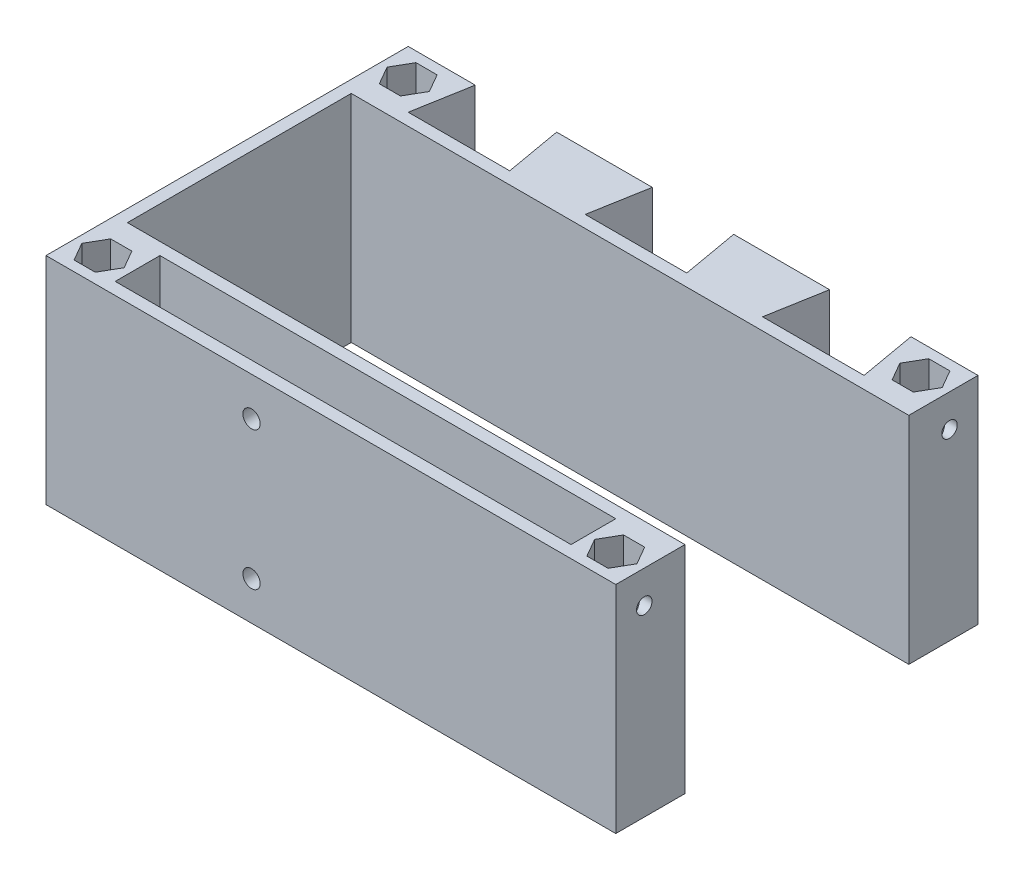
SolidWorks part; units mm, degrees
ref_plane "Front Plane" through (0, 0, 0) normal (0, 0, 1) x (1, 0, 0)
ref_plane "Top Plane" through (0, 0, 0) normal (0, 1, 0) x (1, 0, 0)
ref_plane "Right Plane" through (0, 0, 0) normal (1, 0, 0) x (0, 0, -1)
sketch "Sketch1" plane through (0, 0, 0) normal (0, 1, 0) x (1, 0, 0)
  line L0 (0, 0) -> (140, 0)
  line L1 (140, 0) -> (140, 55)
  line L2 (140, 55) -> (0, 55)
  line L3 (0, 55) -> (0, 0)
  line L4 (140, 58) -> (0, 58)
  line L5 (0, -3) -> (140, -3)
  line L6 (0, 55) -> (0, 58)
  line L7 (0, -3) -> (0, 0)
  line L8 (140, -3) -> (140, 0)
  line L9 (140, 55) -> (140, 58)
  line L10 (0, 27.5) -> (140, 27.5) construction
  line L11 (0, 58) -> (0, 72)
  line L12 (0, 72) -> (14, 72)
  line L13 (14, 72) -> (14, 58)
  line L14 (14, 58) -> (0, 58)
  line L15 (7, 72) -> (7, 58) construction
  line L16 (4.4019, -5.5) -> (9.5981, -5.5)
  line L17 (1.8038, 65) -> (12.1962, 65) construction
  line L18 (12.1962, 65) -> (9.5981, 69.5)
  line L19 (9.5981, 69.5) -> (4.4019, 69.5)
  line L20 (4.4019, 69.5) -> (1.8038, 65)
  line L21 (1.8038, 65) -> (4.4019, 60.5)
  line L22 (4.4019, 60.5) -> (9.5981, 60.5)
  line L23 (9.5981, 60.5) -> (12.1962, 65)
  line L24 (1.8038, -10) -> (12.1962, -10) construction
  line L25 (7, -17) -> (7, -3) construction
  line L26 (9.5981, -5.5) -> (12.1962, -10)
  line L27 (1.8038, -10) -> (4.4019, -5.5)
  line L28 (4.4019, -14.5) -> (1.8038, -10)
  line L29 (9.5981, -14.5) -> (4.4019, -14.5)
  line L30 (12.1962, -10) -> (9.5981, -14.5)
  line L31 (14, -17) -> (14, -3)
  line L32 (0, -17) -> (14, -17)
  line L33 (0, -3) -> (0, -17)
  line L34 (70, 55) -> (70, 0) construction
  line L35 (0, -3) -> (14, -3)
  line L36 (133, -17) -> (133, -3) construction
  line L37 (138.1962, -10) -> (127.8038, -10) construction
  line L38 (140, -3) -> (140, -17)
  line L39 (140, -17) -> (126, -17)
  line L40 (126, -17) -> (126, -3)
  line L41 (127.8038, -10) -> (130.4019, -14.5)
  line L42 (130.4019, -14.5) -> (135.5981, -14.5)
  line L43 (135.5981, -14.5) -> (138.1962, -10)
  line L44 (138.1962, -10) -> (135.5981, -5.5)
  line L45 (130.4019, -5.5) -> (127.8038, -10)
  line L46 (135.5981, -5.5) -> (130.4019, -5.5)
  line L47 (140, -3) -> (126, -3)
  line L48 (135.5981, 60.5) -> (130.4019, 60.5)
  line L49 (138.1962, 65) -> (127.8038, 65) construction
  line L50 (133, 72) -> (133, 58) construction
  line L51 (130.4019, 60.5) -> (127.8038, 65)
  line L52 (138.1962, 65) -> (135.5981, 60.5)
  line L53 (135.5981, 69.5) -> (138.1962, 65)
  line L54 (130.4019, 69.5) -> (135.5981, 69.5)
  line L55 (127.8038, 65) -> (130.4019, 69.5)
  line L56 (126, 72) -> (126, 58)
  line L57 (140, 72) -> (126, 72)
  line L58 (140, 58) -> (140, 72)
  line L59 (14, 72) -> (126, 72)
  line L60 (14, -17) -> (126, -17)
  line L61 (14, 69) -> (126, 69)
  line L62 (14, -14) -> (126, -14)
  line L63 (3, 55) -> (3, 0)
  line L64 (14, 58) -> (16.4686, 72)
  line L65 (36.4686, 72) -> (38.9372, 58)
  line L66 (126, 58) -> (123.5314, 72)
  line L67 (103.5314, 72) -> (101.0628, 58)
  line L68 (57.5, 58) -> (59.9686, 72)
  line L69 (79.9686, 72) -> (82.4372, 58)
  circle A0 centre (7, 65) radius 4.5 construction
  circle A1 centre (7, -10) radius 4.5 construction
  circle A2 centre (133, -10) radius 4.5 construction
  circle A3 centre (133, 65) radius 4.5 construction
  dimension "D6" = 9
  dimension "D1" = 55
  dimension "D2" = 140
  dimension "D4" = 14
  dimension "D5" = 14
  dimension "D7" = 3
  dimension "D8" = 3
  dimension "D9" = 80
  dimension "D10" = 80
  dimension "D11" = 20
  dimension "D12" = 2
  dimension "D3" = 3
extrude "Boss-Extrude2" add sketch "Sketch1" along normal blind 53 contours L62 L31 L60 L40 | L5 L8 L0 L7 | L40 L39 L38 L5 L46 L44 L43 L42 L41 L45 | L5 L33 L32 L31 L26 L30 L29 L28 L27 L16 | L63 L2 L3 L0 | L13 L12 L11 L4 L23 L22 L21 L20 L19 L18 | L2 L9 L4 L6 | L61 L64 L59 L13 | L13 L64 L61 | L4 L68 L61 L65 | L61 L68 L59 L65 | L61 L69 L4 L67 | L59 L69 L61 L67 | L4 L58 L57 L56 L51 L55 L54 L53 L52 L48 | L66 L61 L56 L59 | L66 L56 L61
sketch "Sketch2" plane through (140, 0, 0) normal (1, 0, 0) x (0, 0, -1)
  line L0 (-17, 53) -> (-17, 0) construction
  line L1 (0, 53) -> (-17, 53) construction
  line L3 (27.5, 53) -> (27.5, 0) construction
  line L4 (55, 53) -> (0, 53) construction
  line L5 (55, 0) -> (0, 0) construction
  circle A0 centre (-10, 45) radius 1.9
  circle A1 centre (65, 45) radius 1.9
  dimension "D1" = 3.8
  dimension "D2" = 8
  dimension "D3" = 7
sketch "Sketch3" plane through (0, 0, 0) normal (-1, 0, 0) x (0, 0, 1)
  circle A0 centre (-65, 45) radius 1.9
  circle A1 centre (10, 45) radius 1.9
  dimension "D1" = 3.8
  dimension "D2" = 3.8
extrude "Cut-Extrude1" cut sketch "Sketch2" against normal blind 9.5
extrude "Cut-Extrude2" cut sketch "Sketch3" against normal blind 9.5
sketch "Sketch4" plane through (0, 0, 17) normal (0, 0, 1) x (1, 0, 0)
  line L0 (0, 26.5) -> (140, 26.5) construction
  line L1 (30, 47.5) -> (71, 47.5) construction
  line L2 (30, 47.5) -> (30, 5.5) construction
  line L3 (30, 5.5) -> (71, 5.5) construction
  line L4 (71, 47.5) -> (71, 5.5) construction
  line L5 (0, 53) -> (0, 0) construction
  line L6 (140, 53) -> (140, 0) construction
  line L7 (30, 26.5) -> (71, 26.5) construction
  circle A0 centre (50.5, 43.5) radius 2.125
  circle A1 centre (50.5, 9.5) radius 2.125
  dimension "D5" = 4
  dimension "D6" = 4.25
  dimension "D1" = 42
  dimension "D2" = 41
  dimension "D3" = 30
  dimension "D4" = 20.5
extrude "Cut-Extrude3" cut sketch "Sketch4" against normal up to next
sketch "Sketch5" plane through (0, 0, 0) normal (0, -1, 0) x (1, 0, 0)
  line L0 (3.9042, -59.6379) -> (10.0958, -59.6379)
  line L5 (0, -27.5) -> (63.0541, -27.5) construction
  line L6 (13.1916, 10) -> (10.0958, 15.3621)
  line L7 (70, 17) -> (69.9686, -58) construction
  line L8 (10.0958, 15.3621) -> (3.9042, 15.3621)
  line L9 (12.1962, 10) -> (1.8038, 10) construction
  line L10 (7, 14.5) -> (7, 5.5) construction
  line L11 (9.5981, 14.5) -> (4.4019, 14.5) construction
  line L12 (4.4019, 5.5) -> (9.5981, 5.5) construction
  line L17 (132.9979, 14.4472) -> (132.9903, 5.4472) construction
  line L18 (127.798, 9.9516) -> (138.1903, 9.9429) construction
  line L19 (3.9042, 15.3621) -> (0.8084, 10)
  line L20 (0.8084, 10) -> (3.9042, 4.6379)
  line L21 (3.9042, 4.6379) -> (10.0958, 4.6379)
  line L22 (10.0958, 4.6379) -> (13.1916, 10)
  line L23 (10.0958, -59.6379) -> (13.1916, -65)
  line L24 (13.1916, -65) -> (10.0958, -70.3621)
  line L25 (10.0958, -70.3621) -> (3.9042, -70.3621)
  line L26 (3.9042, -70.3621) -> (0.8084, -65)
  line L27 (0.8084, -65) -> (3.9042, -59.6379)
  line L28 (139.1229, -65.0579) -> (136.0316, -59.6933)
  line L29 (136.0226, -70.4174) -> (139.1229, -65.0579)
  line L30 (129.831, -70.4122) -> (136.0226, -70.4174)
  line L31 (126.7397, -65.0476) -> (129.831, -70.4122)
  line L32 (129.84, -59.6881) -> (126.7397, -65.0476)
  line L33 (136.0316, -59.6933) -> (129.84, -59.6881)
  line L34 (129.8938, 4.5877) -> (126.8025, 9.9524)
  line L35 (136.0854, 4.5825) -> (129.8938, 4.5877)
  line L36 (139.1857, 9.942) -> (136.0854, 4.5825)
  line L37 (136.0944, 15.3067) -> (139.1857, 9.942)
  line L38 (129.9028, 15.3119) -> (136.0944, 15.3067)
  line L39 (126.8025, 9.9524) -> (129.9028, 15.3119)
  circle A0 centre (7, 10) radius 2.75
  circle A1 centre (7, -65) radius 2.75
  circle A2 centre (132.9313, -65.0528) radius 2.75
  circle A3 centre (132.9941, 9.9472) radius 2.75
  circle A4 centre (7, 10) radius 5.3621 construction
  circle A5 centre (132.9941, 9.9472) radius 5.3621 construction
  dimension "D1" = 5.5
extrude "Boss-Extrude6" add sketch "Sketch5" against normal blind 12
